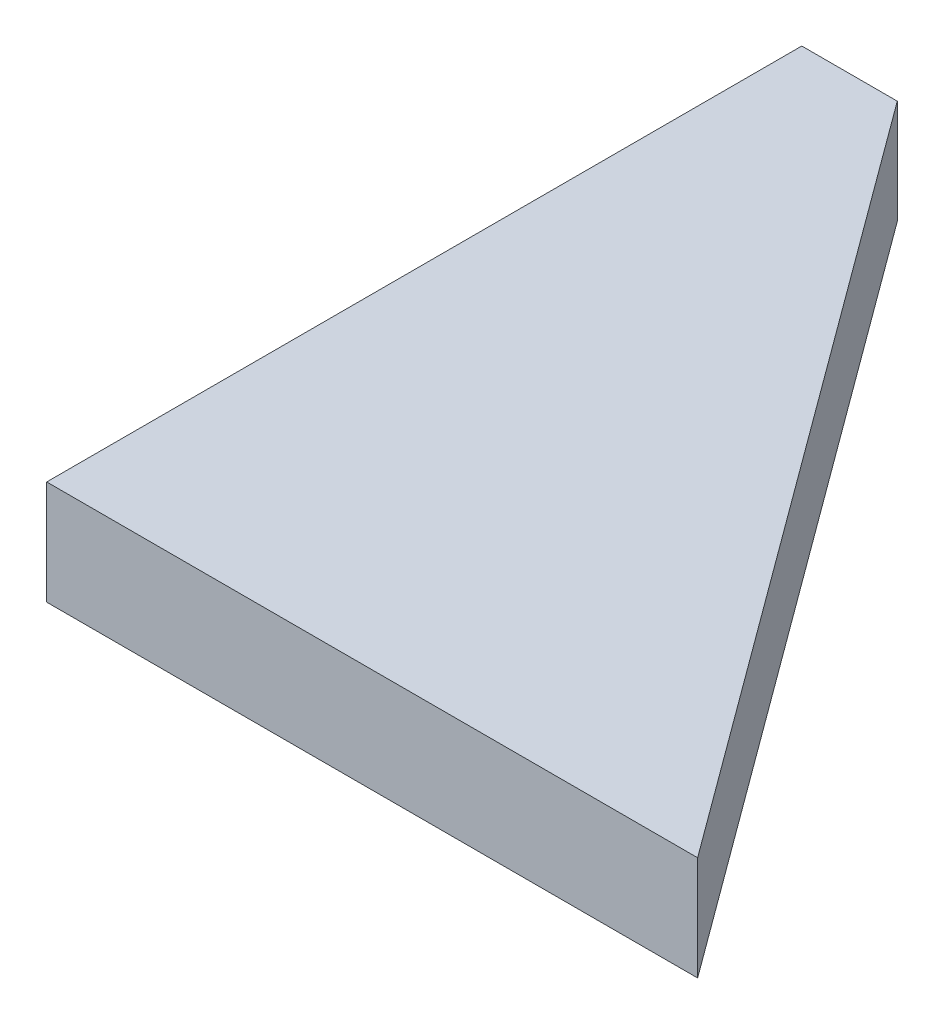
SolidWorks part; units mm, degrees
ref_plane "Спереди" through (0, 0, 0) normal (0, 0, 1) x (1, 0, 0)
ref_plane "Сверху" through (0, 0, 0) normal (0, 1, 0) x (1, 0, 0)
ref_plane "Справа" through (0, 0, 0) normal (1, 0, 0) x (0, 0, -1)
sketch "Эскиз1" plane through (0, 0, 0) normal (0, 1, 0) x (1, 0, 0)
  line L0 (0, 1.475) -> (0, 30.475)
  line L1 (0, 30.475) -> (3.6687, 30.475)
  line L2 (3.6687, 30.475) -> (25, 1.475)
  line L3 (25, 1.475) -> (0, 1.475)
extrude "Бобышка-Вытянуть1" add sketch "Эскиз1" along normal blind 4
